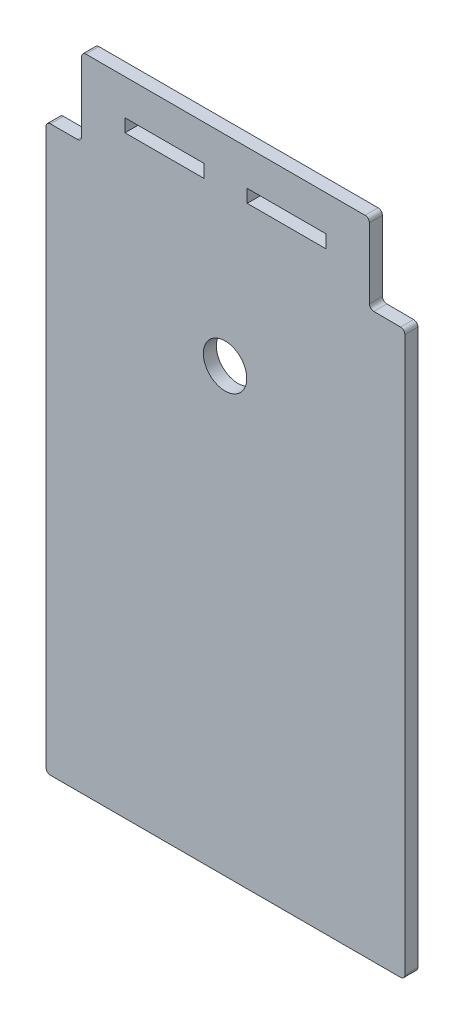
SolidWorks part; units mm, degrees
ref_plane "Alzado" through (0, 0, 0) normal (0, 0, 1) x (1, 0, 0)
ref_plane "Planta" through (0, 0, 0) normal (0, 1, 0) x (1, 0, 0)
ref_plane "Vista lateral" through (0, 0, 0) normal (1, 0, 0) x (0, 0, -1)
sketch "Model" plane through (0, 0, 0) normal (0, 0, 1) x (1, 0, 0)
  line L0 (95.9977, -24.0179) -> (95.9977, 103.7647)
  line L1 (14.3249, -25.0179) -> (94.9977, -25.0179)
  line L2 (13.3249, 21.2979) -> (13.3249, -24.0179)
  line L3 (13.3249, 53.9821) -> (13.3249, 21.2979)
  line L4 (13.3249, 53.9821) -> (13.3249, 59.9821)
  line L5 (22.4977, 122.9821) -> (86.8249, 122.9821)
  line L6 (59.6613, 114.7821) -> (59.6613, 111.7821)
  line L7 (77.8249, 114.7821) -> (59.6613, 114.7821)
  line L8 (77.8249, 111.7821) -> (77.8249, 114.7821)
  line L9 (59.6613, 111.7821) -> (77.8249, 111.7821)
  line L10 (49.6613, 111.7821) -> (49.6613, 114.7821)
  line L11 (31.4977, 111.7821) -> (49.6613, 111.7821)
  line L12 (31.4977, 114.7821) -> (31.4977, 111.7821)
  line L13 (49.6613, 114.7821) -> (31.4977, 114.7821)
  line L14 (13.3249, 103.9821) -> (13.3249, 59.9821)
  line L15 (88.8303, 104.8025) -> (95.003, 104.77)
  line L16 (20.4977, 104.9821) -> (14.3249, 104.9821)
  line L17 (87.8249, 121.9821) -> (87.8355, 105.8077)
  line L18 (21.4977, 121.9821) -> (21.4977, 105.9821)
  arc A0 (94.9977, -25.0179) -> (95.9977, -24.0179) centre (94.9977, -24.0179) ccw
  arc A1 (13.3249, -24.0179) -> (14.3249, -25.0179) centre (14.3249, -24.0179) ccw
  arc A2 (87.8249, 121.9821) -> (86.8249, 122.9821) centre (86.8249, 121.9821) ccw
  arc A3 (22.4977, 122.9821) -> (21.4977, 121.9821) centre (22.4977, 121.9821) ccw
  circle A4 centre (54.5613, 76.7821) radius 5
  arc A5 (95.9977, 103.7647) -> (95.003, 104.77) centre (94.9977, 103.77) ccw
  arc A6 (14.3249, 104.9821) -> (13.3249, 103.9821) centre (14.3249, 103.9821) ccw
  arc A7 (87.8355, 105.8077) -> (88.8303, 104.8025) centre (88.8355, 105.8024) ccw
  arc A8 (20.4977, 104.9821) -> (21.4977, 105.9821) centre (20.4977, 105.9821) ccw
extrude "Saliente-Extruir1" add sketch "Model" along normal blind 3
